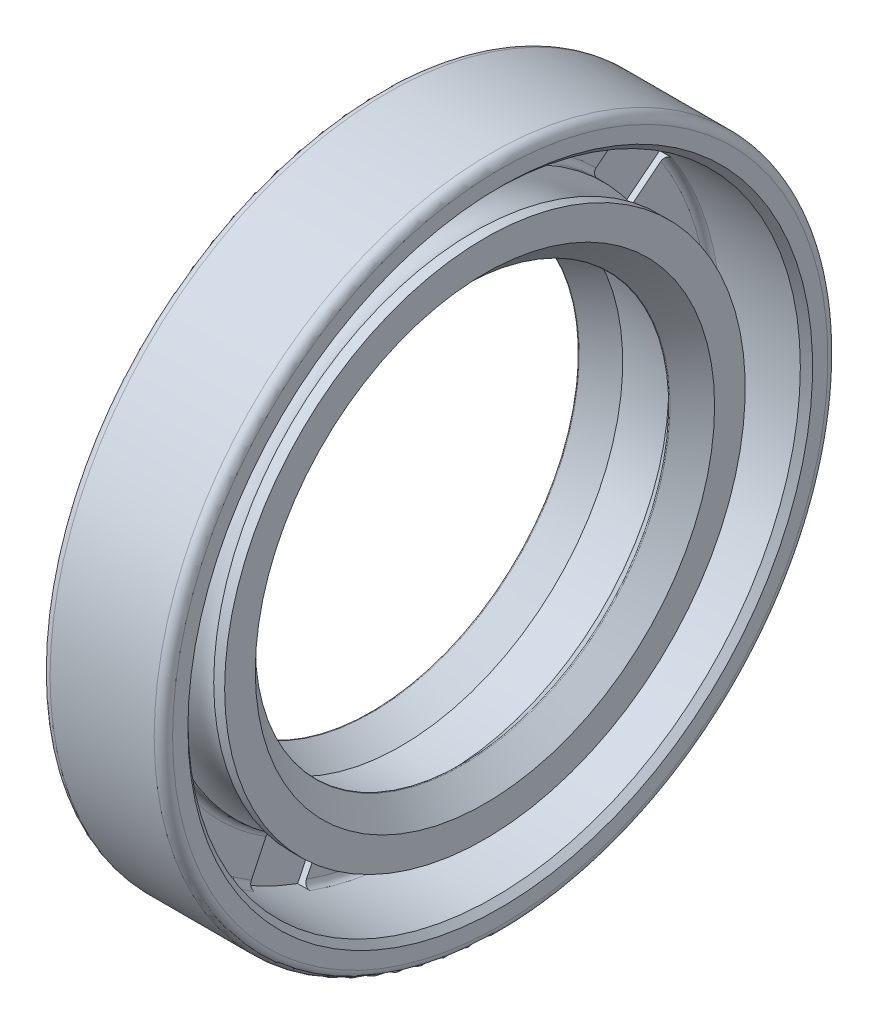
SolidWorks part; units mm, degrees
material "Резина"
ref_plane "Спереди" through (0, 0, 0) normal (0, 0, 1) x (1, 0, 0)
ref_plane "Сверху" through (0, 0, 0) normal (0, 1, 0) x (1, 0, 0)
ref_plane "Справа" through (0, 0, 0) normal (1, 0, 0) x (0, 0, -1)
sketch "Эскиз1" plane through (0, 0, 0) normal (0, 0, 1) x (1, 0, 0)
  line L0 (0, 0) -> (4, 0) construction
  line L1 (3.8, 10) -> (4, 10.2)
  line L2 (0.1, 7.4) -> (0.1, 7.5)
  line L3 (0.1, 7.5) -> (0, 7.5)
  line L4 (0, 7.5) -> (0, 10.7)
  line L5 (0.1, 7.4) -> (-0.2263, 6.8069)
  line L6 (-0.1862, 6.7658) -> (0.75, 7.25)
  line L7 (0.75, 7.25) -> (2.25, 7.25)
  line L8 (2.25, 7.25) -> (2.7288, 6.7712)
  line L9 (2.7712, 6.7712) -> (3.5, 7.5)
  line L10 (3.5, 7.5) -> (3.5, 8.5)
  line L11 (3.5, 8.5) -> (3.143, 8.5)
  line L12 (1, 8.7) -> (1, 9.8)
  line L13 (1.2, 10) -> (3.8, 10)
  line L14 (4, 10.2) -> (4, 10.7)
  line L15 (0.3, 11) -> (3.7, 11)
  line L16 (2.25, 7.25) -> (2.25, 8.95) construction
  line L17 (2.75, 6.75) -> (2.75, 7.5) construction
  line L18 (1.357, 8.5) -> (1.2, 8.5)
  arc A0 (-0.2263, 6.8069) -> (-0.1862, 6.7658) centre (-0.2, 6.7924) ccw
  arc A1 (2.7288, 6.7712) -> (2.7712, 6.7712) centre (2.75, 6.7924) ccw
  arc A2 (3.7, 11) -> (4, 10.7) centre (3.7, 10.7) cw
  arc A3 (0, 10.7) -> (0.3, 11) centre (0.3, 10.7) cw
  arc A4 (1, 9.8) -> (1.2, 10) centre (1.2, 9.8) cw
  arc A5 (1.2, 8.5) -> (1, 8.7) centre (1.2, 8.7) cw
  arc A6 (1.357, 8.5) -> (3.143, 8.5) centre (2.25, 8.95) ccw
  point P3 (0, 0)
  point P17 (4, 10)
  point P21 (0, 0)
  point P25 (4, 11)
  point P31 (1, 10)
  point P37 (1, 8.5)
  point P40 (0, 0)
  point P42 (0, 0)
  point P43 (0, 7.5208)
  point P44 (0, 0)
  dimension "D15" = 0.03
  dimension "D12" = 0.03
  dimension "D16" = 0.3
  dimension "D18" = 0.2
  dimension "D19" = 2
  dimension "D1" = 4
  dimension "D2" = 0.5
  dimension "D3" = 0.1
  dimension "D4" = 6.75
  dimension "D5" = 11
  dimension "D6" = 1
  dimension "D7" = 1.5
  dimension "D8" = 3
  dimension "D9" = 90
  dimension "D10" = 45
  dimension "D11" = 0.3
  dimension "D13" = 1
  dimension "D14" = 2.5
  dimension "D17" = 1.5
  dimension "D20" = 1.7
revolve "Повернуть1" add sketch "Эскиз1" angle 360 about L0
sketch "Эскиз2" plane through (0, 0, 0) normal (-1, 0, 0) x (0, 0, 1)
  line L0 (0, 0) -> (0, 10.4) construction
  line L1 (-1, 10.3518) -> (-1, 8.8518)
  line L2 (1, 10.3518) -> (1, 8.8518)
  line L3 (0, 0) -> (8.131, 6.4843) construction
  line L4 (7.4699, 7.2361) -> (6.2971, 6.3008)
  line L5 (8.7169, 5.6724) -> (7.5441, 4.7372)
  line L6 (0, 0) -> (10.1393, -2.3142) construction
  line L7 (10.3148, -1.3286) -> (8.8524, -0.9948)
  line L8 (9.8697, -3.2784) -> (8.4074, -2.9446)
  line L9 (0, 0) -> (4.5124, -9.3701) construction
  line L10 (5.3925, -8.8928) -> (4.7416, -7.5413)
  line L11 (3.5905, -9.7605) -> (2.9397, -8.4091)
  line L12 (0, 0) -> (-4.5124, -9.3701) construction
  line L13 (-3.5905, -9.7605) -> (-2.9397, -8.4091)
  line L14 (-5.3925, -8.8928) -> (-4.7416, -7.5413)
  line L15 (0, 0) -> (-10.1393, -2.3142) construction
  line L16 (-9.8697, -3.2784) -> (-8.4074, -2.9446)
  line L17 (-10.3148, -1.3286) -> (-8.8524, -0.9948)
  line L18 (0, 0) -> (-8.131, 6.4843) construction
  line L19 (-8.7169, 5.6724) -> (-7.5441, 4.7372)
  line L20 (-7.4699, 7.2361) -> (-6.2971, 6.3008)
  arc A0 (6.9947, 2.7063) -> (4.1949, 6.2171) centre (0, 0) ccw
  circle A1 centre (0, 0) radius 7.5 construction
  circle A2 centre (0, 0) radius 10.4
  arc A3 (1, 10.3518) -> (-1, 10.3518) centre (0, 0) ccw
  arc A4 (2.2452, 7.156) -> (-2.2452, 7.156) centre (0, 0) ccw
  arc A5 (-2.2452, 7.156) -> (-1, 8.8518) centre (-2.7773, 8.8518) ccw
  arc A6 (2.2452, 7.156) -> (1, 8.8518) centre (2.7773, 8.8518) cw
  arc A7 (4.1949, 6.2171) -> (6.2971, 6.3008) centre (5.189, 7.6904) ccw
  arc A8 (8.7169, 5.6724) -> (7.4699, 7.2361) centre (0, 0) ccw
  arc A9 (6.9947, 2.7063) -> (7.5441, 4.7372) centre (8.6522, 3.3477) cw
  arc A10 (6.477, -3.7813) -> (7.4762, 0.5966) centre (0, 0) ccw
  arc A11 (7.4762, 0.5966) -> (8.8524, -0.9948) centre (9.2479, 0.7379) ccw
  arc A12 (9.8697, -3.2784) -> (10.3148, -1.3286) centre (0, 0) ccw
  arc A13 (6.477, -3.7813) -> (8.4074, -2.9446) centre (8.0119, -4.6774) cw
  arc A14 (1.082, -7.4215) -> (5.1278, -5.4732) centre (0, 0) ccw
  arc A15 (5.1278, -5.4732) -> (4.7416, -7.5413) centre (6.3429, -6.7702) ccw
  arc A16 (3.5905, -9.7605) -> (5.3925, -8.8928) centre (0, 0) ccw
  arc A17 (1.082, -7.4215) -> (2.9397, -8.4091) centre (1.3384, -9.1802) cw
  arc A18 (-5.1278, -5.4732) -> (-1.082, -7.4215) centre (0, 0) ccw
  arc A19 (-1.082, -7.4215) -> (-2.9397, -8.4091) centre (-1.3384, -9.1802) ccw
  arc A20 (-5.3925, -8.8928) -> (-3.5905, -9.7605) centre (0, 0) ccw
  arc A21 (-5.1278, -5.4732) -> (-4.7416, -7.5413) centre (-6.3429, -6.7702) cw
  arc A22 (-7.4762, 0.5966) -> (-6.477, -3.7813) centre (0, 0) ccw
  arc A23 (-6.477, -3.7813) -> (-8.4074, -2.9446) centre (-8.0119, -4.6774) ccw
  arc A24 (-10.3148, -1.3286) -> (-9.8697, -3.2784) centre (0, 0) ccw
  arc A25 (-7.4762, 0.5966) -> (-8.8524, -0.9948) centre (-9.2479, 0.7379) cw
  arc A26 (-4.1949, 6.2171) -> (-6.9947, 2.7063) centre (0, 0) ccw
  arc A27 (-6.9947, 2.7063) -> (-7.5441, 4.7372) centre (-8.6522, 3.3477) ccw
  arc A28 (-7.4699, 7.2361) -> (-8.7169, 5.6724) centre (0, 0) ccw
  arc A29 (-4.1949, 6.2171) -> (-6.2971, 6.3008) centre (-5.189, 7.6904) cw
  point P69 (0, 0)
  dimension "D2" = 2
  dimension "D3" = 1.5
  dimension "D1" = 0.3
  dimension "D4" = 7
extrude "Вырез-Вытянуть1" cut sketch "Эскиз2" against normal blind 0.1
sketch "Эскиз3" plane through (0, 0, 0) normal (-1, 0, 0) x (0, 0, 1)
  circle A2 centre (0, 0) radius 8.4
  circle A3 centre (0, 0) radius 8.4 construction
  text T0 "XJKD        TC           14           22            4              5  " font "Century Gothic" height 1.3
  dimension "D1" = 1
extrude "Бобышка-Вытянуть1" add sketch "Эскиз3" along normal blind 0.1
sketch "Эскиз4" plane through (1, 0, 0) normal (1, 0, 0) x (0, 0, -1)
  line L0 (0, 0) -> (0, 10) construction
  line L1 (-1, 9.9499) -> (-1, 8.441)
  line L2 (1, 9.9499) -> (1, 8.441)
  line L3 (0, 0) -> (7.8183, 6.2349) construction
  line L4 (7.1556, 6.9855) -> (5.9759, 6.0447)
  line L5 (8.4026, 5.4218) -> (7.2229, 4.481)
  line L6 (0, 0) -> (9.7493, -2.2252) construction
  line L7 (9.9229, -1.2391) -> (8.4519, -0.9034)
  line L8 (9.4779, -3.189) -> (8.0068, -2.8532)
  line L9 (0, 0) -> (4.3388, -9.0097) construction
  line L10 (5.2181, -8.5306) -> (4.5634, -7.1712)
  line L11 (3.4161, -9.3984) -> (2.7614, -8.0389)
  line L12 (0, 0) -> (-4.3388, -9.0097) construction
  line L13 (-3.4161, -9.3984) -> (-2.7614, -8.0389)
  line L14 (-5.2181, -8.5306) -> (-4.5634, -7.1712)
  line L15 (0, 0) -> (-9.7493, -2.2252) construction
  line L16 (-9.4779, -3.189) -> (-8.0068, -2.8532)
  line L17 (-9.9229, -1.2391) -> (-8.4519, -0.9034)
  line L18 (0, 0) -> (-7.8183, 6.2349) construction
  line L19 (-8.4026, 5.4218) -> (-7.2229, 4.481)
  line L20 (-7.1556, 6.9855) -> (-5.9759, 6.0447)
  circle A0 centre (0, 0) radius 10 construction
  circle A1 centre (0, 0) radius 8.5 construction
  arc A2 (1, 9.9499) -> (-1, 9.9499) centre (0, 0) ccw
  arc A3 (1, 8.441) -> (-1, 8.441) centre (0, 0) ccw
  arc A4 (7.2229, 4.481) -> (5.9759, 6.0447) centre (0, 0) ccw
  arc A5 (8.4026, 5.4218) -> (7.1556, 6.9855) centre (0, 0) ccw
  arc A6 (8.0068, -2.8532) -> (8.4519, -0.9034) centre (0, 0) ccw
  arc A7 (9.4779, -3.189) -> (9.9229, -1.2391) centre (0, 0) ccw
  arc A8 (2.7614, -8.0389) -> (4.5634, -7.1712) centre (0, 0) ccw
  arc A9 (3.4161, -9.3984) -> (5.2181, -8.5306) centre (0, 0) ccw
  arc A10 (-4.5634, -7.1712) -> (-2.7614, -8.0389) centre (0, 0) ccw
  arc A11 (-5.2181, -8.5306) -> (-3.4161, -9.3984) centre (0, 0) ccw
  arc A12 (-8.4519, -0.9034) -> (-8.0068, -2.8532) centre (0, 0) ccw
  arc A13 (-9.9229, -1.2391) -> (-9.4779, -3.189) centre (0, 0) ccw
  arc A14 (-5.9759, 6.0447) -> (-7.2229, 4.481) centre (0, 0) ccw
  arc A15 (-7.1556, 6.9855) -> (-8.4026, 5.4218) centre (0, 0) ccw
  point P40 (0, 0)
  dimension "D1" = 2
  dimension "D2" = 7
extrude "Вырез-Вытянуть2" cut sketch "Эскиз4" against normal blind 0.2 and the other way blind 0.3
